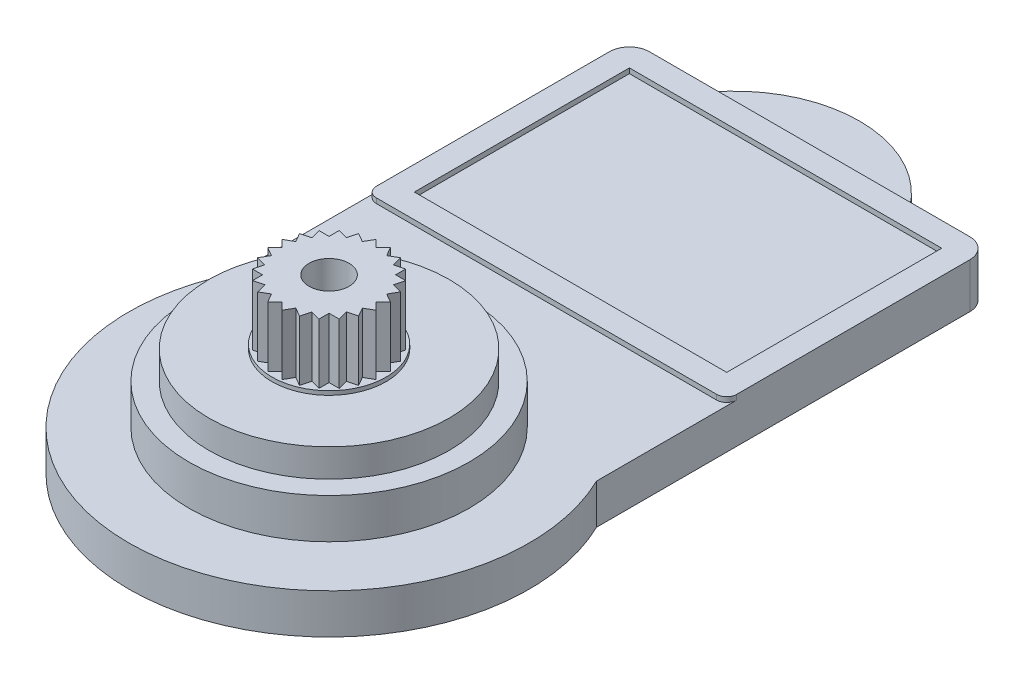
SolidWorks part; units mm, degrees
material "Magnesium Alloy"
ref_plane "Front Plane" through (0, 0, 0) normal (0, 0, 1) x (1, 0, 0)
ref_plane "Top Plane" through (0, 0, 0) normal (0, 1, 0) x (1, 0, 0)
ref_plane "Right Plane" through (0, 0, 0) normal (1, 0, 0) x (0, 0, -1)
sketch "Sketch1" plane through (0, 0, 0) normal (0, 1, 0) x (1, 0, 0)
  line L0 (-9, 13.05) -> (9, 13.05)
  line L1 (8, -17.55) -> (-8, -17.55)
  line L2 (9, -16.55) -> (9, 16.55)
  line L3 (8, 17.55) -> (-8, 17.55)
  line L4 (-9, -16.55) -> (-9, 16.55)
  line L5 (9, -17.55) -> (-9, 17.55) construction
  line L6 (9, 17.55) -> (-9, -17.55) construction
  line L7 (0, 13.05) -> (0, 19.559) construction
  line L8 (0, 15.55) -> (-4.0271, 15.55) construction
  arc A0 (-9, -16.55) -> (-8, -17.55) centre (-8, -16.55) ccw
  arc A1 (8, -17.55) -> (9, -16.55) centre (8, -16.55) ccw
  arc A2 (9, 16.55) -> (8, 17.55) centre (8, 16.55) ccw
  arc A3 (-8, 17.55) -> (-9, 16.55) centre (-8, 16.55) ccw
  circle A4 centre (0, -10.95) radius 10
  arc A5 (-5, 13.05) -> (5, 13.05) centre (0, 9.3) cw
  circle A6 centre (-8, 12.05) radius 1
  circle A7 centre (8, 12.05) radius 1
  point P2 (0, 0)
  dimension "D3" = 1
  dimension "D5" = 4.5
  dimension "D6" = 5
  dimension "D7" = 20
  dimension "D2" = 24
  dimension "D9" = 2.5
  dimension "D1" = 18
  dimension "D4" = 6.6
  dimension "D8" = 5
extrude "Boss-Extrude1" add sketch "Sketch1" along normal blind 2 contours A4 | L4 A4 | L2 A4 | L1 A4 | A7 L0 A6 L4 A4 L2 | A6 | A5 L0 | A7 A4
sketch "Sketch2" plane through (0, 2, 0) normal (0, 1, 0) x (-1, 0, 0)
  line L0 (-9, 6.5911) -> (-9, -12.05) construction
  line L1 (9, -13.05) -> (-9, -13.05)
  line L2 (9, -13.05) -> (9, -0.41)
  line L3 (8.5, 0.09) -> (-8.5, 0.09)
  line L4 (-9, -13.05) -> (-9, -0.41)
  circle A0 centre (8, -12.05) radius 1
  circle A1 centre (-8, -12.05) radius 1
  arc A2 (9, -0.41) -> (8.5, 0.09) centre (8.5, -0.41) ccw
  arc A3 (-9, -0.41) -> (-8.5, 0.09) centre (-8.5, -0.41) cw
  point P14 (9, 0.09)
  point P17 (-9, 0.09)
  line M1 (9, -12.05) -> (9, 6.5911)
  line M3 (-9, 6.5911) -> (-9, -12.05)
  arc M4 (-9, -12.05) -> (-8, -13.05) centre (-8, -12.05) ccw
  line M5 (-8, -13.05) -> (-5, -13.05)
  line M7 (5, -13.05) -> (8, -13.05)
  arc M8 (8, -13.05) -> (9, -12.05) centre (8, -12.05) ccw
  dimension "D2" = 0.5
  dimension "D1" = 13.14
extrude "Boss-Extrude2" add sketch "Sketch2" along normal blind 0.25 contours A1 L1 A0 L3 M5 M7 M1 M3 | A0 M8 | A1 M4
sketch "Sketch3" plane through (0, 2.25, 0) normal (0, 1, 0) x (-1, 0, 0)
  line L52 (-7.8, -11.85) -> (7.8, -11.85)
  line L53 (7.8, -11.85) -> (7.8, -1.11)
  line L54 (-7.8, -1.11) -> (-7.8, -11.85)
  line L55 (7.8, -1.11) -> (-7.8, -1.11)
  line L56 (-7.8, -11.85) -> (7.8, -11.85)
  line L57 (7.8, -11.85) -> (7.8, -1.11)
  line L58 (-7.8, -1.11) -> (-7.8, -11.85)
  line L59 (7.8, -1.11) -> (-7.8, -1.11)
  dimension "D1" = 1.2
extrude "Cut-Extrude1" cut sketch "Sketch3" against normal blind 0.25
sketch "Sketch4" plane through (0, 2, 0) normal (0, 1, 0) x (-1, 0, 0)
  circle A0 centre (0, 10.95) radius 7
  dimension "D1" = 14
extrude "Boss-Extrude3" add sketch "Sketch4" along normal blind 2
sketch "Sketch5" plane through (0, 4, 0) normal (0, 1, 0) x (-1, 0, 0)
  circle A0 centre (0, 10.95) radius 6
extrude "Boss-Extrude4" add sketch "Sketch5" along normal blind 1.4
sketch "Sketch6" plane through (0, 5.4, 0) normal (0, 1, 0) x (-1, 0, 0)
  circle A0 centre (0, 10.95) radius 2.85
  dimension "D1" = 5.7
extrude "Boss-Extrude5" add sketch "Sketch6" along normal blind 0.2
sketch "Sketch9" plane through (0, 5.6, 0) normal (0, 1, 0) x (-1, 0, 0)
  line L0 (0, 8.1) -> (0, 8.6)
  line L1 (0, 8.6) -> (0.4623, 8.1377)
  line L2 (0, 8.6) -> (-0.4623, 8.1377)
  line L3 (-0.6082, 8.6801) -> (-0.2814, 8.1139)
  line L4 (-0.6082, 8.6801) -> (-1.1744, 8.3532)
  line L5 (-1.175, 8.9148) -> (-1.0058, 8.2834)
  line L6 (-1.175, 8.9148) -> (-1.8065, 8.7456)
  line L7 (-1.6617, 9.2883) -> (-1.6617, 8.6346)
  line L8 (-1.6617, 9.2883) -> (-2.3154, 9.2883)
  line L9 (-2.0352, 9.775) -> (-2.2044, 9.1435)
  line L10 (-2.0352, 9.775) -> (-2.6666, 9.9442)
  line L11 (-2.2699, 10.3418) -> (-2.5968, 9.7756)
  line L12 (-2.2699, 10.3418) -> (-2.8361, 10.6686)
  line L13 (-2.35, 10.95) -> (-2.8123, 10.4877)
  line L14 (-2.35, 10.95) -> (-2.8123, 11.4123)
  line L15 (-2.2699, 11.5582) -> (-2.8361, 11.2314)
  line L16 (-2.2699, 11.5582) -> (-2.5968, 12.1244)
  line L17 (-2.0352, 12.125) -> (-2.6666, 11.9558)
  line L18 (-2.0352, 12.125) -> (-2.2044, 12.7565)
  line L19 (-1.6617, 12.6117) -> (-2.3154, 12.6117)
  line L20 (-1.6617, 12.6117) -> (-1.6617, 13.2654)
  line L21 (-1.175, 12.9852) -> (-1.8065, 13.1544)
  line L22 (-1.175, 12.9852) -> (-1.0058, 13.6166)
  line L23 (-0.6082, 13.2199) -> (-1.1744, 13.5468)
  line L24 (-0.6082, 13.2199) -> (-0.2814, 13.7861)
  line L25 (0, 13.3) -> (-0.4623, 13.7623)
  line L26 (0, 13.3) -> (0.4623, 13.7623)
  line L27 (0.6082, 13.2199) -> (0.2814, 13.7861)
  line L28 (0.6082, 13.2199) -> (1.1744, 13.5468)
  line L29 (1.175, 12.9852) -> (1.0058, 13.6166)
  line L30 (1.175, 12.9852) -> (1.8065, 13.1544)
  line L31 (1.6617, 12.6117) -> (1.6617, 13.2654)
  line L32 (1.6617, 12.6117) -> (2.3154, 12.6117)
  line L33 (2.0352, 12.125) -> (2.2044, 12.7565)
  line L34 (2.0352, 12.125) -> (2.6666, 11.9558)
  line L35 (2.2699, 11.5582) -> (2.5968, 12.1244)
  line L36 (2.2699, 11.5582) -> (2.8361, 11.2314)
  line L37 (2.35, 10.95) -> (2.8123, 11.4123)
  line L38 (2.35, 10.95) -> (2.8123, 10.4877)
  line L39 (2.2699, 10.3418) -> (2.8361, 10.6686)
  line L40 (2.2699, 10.3418) -> (2.5968, 9.7756)
  line L41 (2.0352, 9.775) -> (2.6666, 9.9442)
  line L42 (2.0352, 9.775) -> (2.2044, 9.1435)
  line L43 (1.6617, 9.2883) -> (2.3154, 9.2883)
  line L44 (1.6617, 9.2883) -> (1.6617, 8.6346)
  line L45 (1.175, 8.9148) -> (1.8065, 8.7456)
  line L46 (1.175, 8.9148) -> (1.0058, 8.2834)
  line L47 (0.6082, 8.6801) -> (1.1744, 8.3532)
  line L48 (0.6082, 8.6801) -> (0.2814, 8.1139)
  circle A0 centre (0, 10.95) radius 2.85
  circle A1 centre (0, 10.95) radius 2.85 construction
  dimension "D1" = 0.5
  dimension "D2" = 45
extrude "Boss-Extrude6" add sketch "Sketch9" along normal blind 3 contours L48 L47 L46 L45 L44 L43 L42 L41 L40 L39 L38 L37 L36 L35 L34 L33 L32 L31 L30 L29 L28 L27 L26 L25 L24 L23 L22 L21 L20 L19 L18 L17 L16 L15 L14 L13 L12 L11 L10 L9 L8 L7 L6 L5 L4 L3 L2 L1
sketch "Sketch10" plane through (0, 8.6, 0) normal (0, 1, 0) x (-1, 0, 0)
  circle A0 centre (0, 10.95) radius 1
  dimension "D1" = 2
extrude "Cut-Extrude4" cut sketch "Sketch10" against normal blind 3
